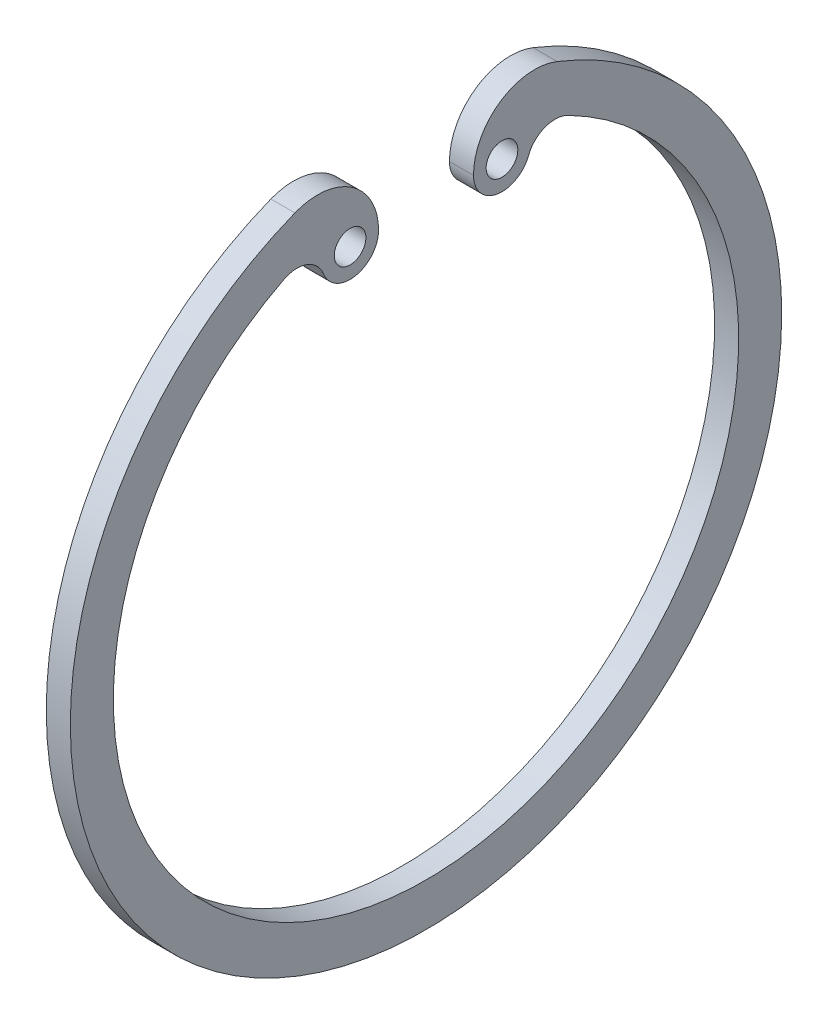
SolidWorks part; units mm, degrees
material "AISI Тип A2 Инструментальная сталь"
ref_plane "Спереди" through (0, 0, 0) normal (0, 0, 1) x (1, 0, 0)
ref_plane "Сверху" through (0, 0, 0) normal (0, 1, 0) x (1, 0, 0)
ref_plane "Справа" through (0, 0, 0) normal (1, 0, 0) x (0, 0, -1)
sketch "Эскиз1" plane through (0, 0, 0) normal (1, 0, 0) x (0, 0, -1)
  line L0 (0, -1000) -> (0, 49000) construction
  arc A0 (-10.3576, 26.1214) -> (10.3576, 26.1214) centre (0, 0) ccw
  arc A1 (-11.2156, 22.0068) -> (11.2156, 22.0068) centre (0, 0) ccw
  circle A2 centre (-6, 21.6334) radius 1.25
  arc A3 (-8.097, 20.8178) -> (-3.75, 21.6334) centre (-6, 21.6334) ccw
  arc A4 (-10.3576, 26.1214) -> (-3.75, 21.6334) centre (-8.578, 21.6334) cw
  arc A5 (-11.2156, 22.0068) -> (-8.097, 20.8178) centre (-10.1939, 20.0022) cw
  circle A6 centre (6, 21.6334) radius 1.25
  arc A7 (11.2156, 22.0068) -> (8.097, 20.8178) centre (10.1939, 20.0022) ccw
  arc A8 (8.097, 20.8178) -> (3.75, 21.6334) centre (6, 21.6334) cw
  arc A9 (10.3576, 26.1214) -> (3.75, 21.6334) centre (8.578, 21.6334) ccw
  dimension "D1" = 56.2
  dimension "D3" = 2.5
  dimension "D2" = 24.7
  dimension "D4" = 1
  dimension "D5" = 6
extrude "Бобышка-Вытянуть1" add sketch "Эскиз1" along normal blind 1.9
equation "\"D2@Эскиз1\"=49.4/2"
